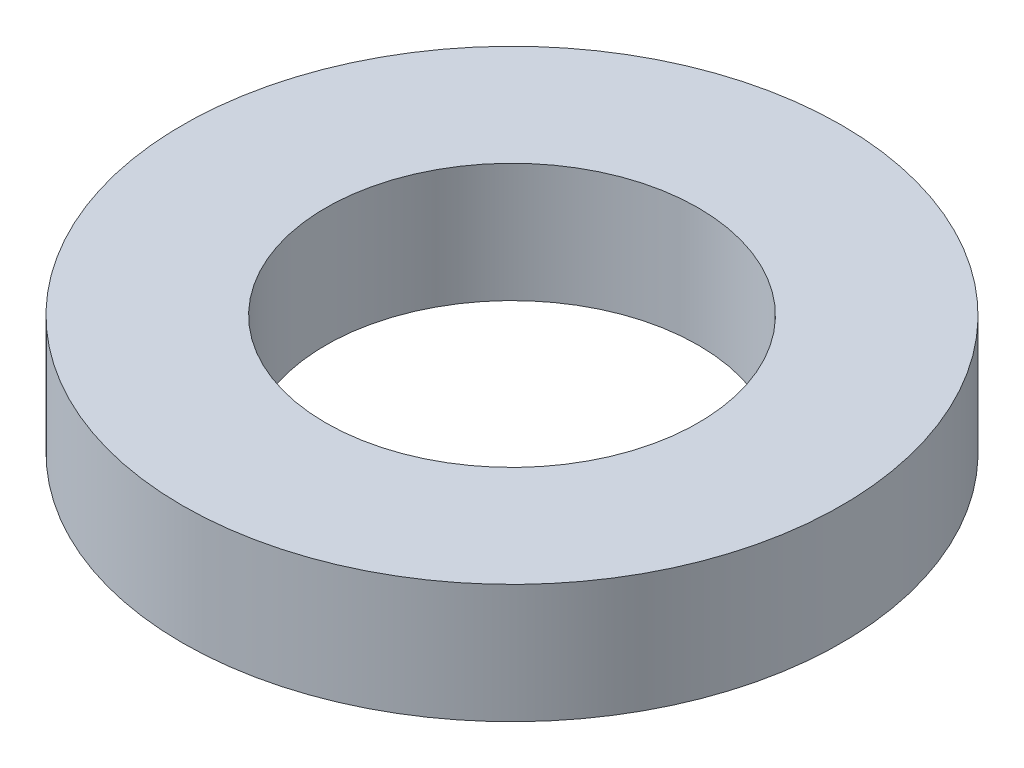
SolidWorks part; units mm, degrees
material "Nylon 101"
ref_plane "Front Plane" through (0, 0, 0) normal (0, 0, 1) x (1, 0, 0)
ref_plane "Top Plane" through (0, 0, 0) normal (0, 1, 0) x (1, 0, 0)
ref_plane "Right Plane" through (0, 0, 0) normal (1, 0, 0) x (0, 0, -1)
sketch "Sketch1" plane through (0, 0, 0) normal (0, 1, 0) x (1, 0, 0)
  circle A0 centre (0, 0) radius 5.842
  circle A1 centre (0, 0) radius 3.302
  dimension "D1" = 6.604
  dimension "D2" = 11.684
extrude "Boss-Extrude1" add sketch "Sketch1" along normal blind 2.1082
